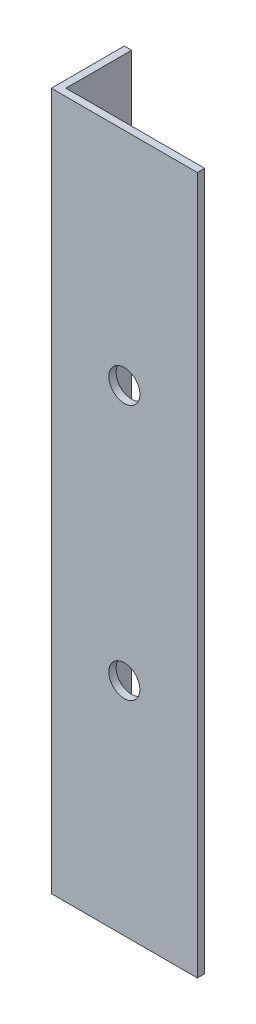
SolidWorks part; units mm, degrees
material "1060 Сплав"
ref_plane "Спереди" through (0, 0, 0) normal (0, 0, 1) x (1, 0, 0)
ref_plane "Сверху" through (0, 0, 0) normal (0, 1, 0) x (1, 0, 0)
ref_plane "Справа" through (0, 0, 0) normal (1, 0, 0) x (0, 0, -1)
sketch "Эскиз1" plane through (0, 0, 0) normal (0, 1, 0) x (1, 0, 0)
  line L0 (0, 0) -> (0, 20)
  line L1 (0, 20) -> (2, 20)
  line L2 (2, 20) -> (2, 2)
  line L3 (2, 2) -> (40, 2)
  line L4 (40, 2) -> (40, 0)
  line L5 (40, 0) -> (0, 0)
  dimension "D1" = 2
  dimension "D2" = 40
  dimension "D3" = 20
extrude "Бобышка-Вытянуть1" add sketch "Эскиз1" along normal blind 191
sketch "Эскиз2" plane through (0, 0, 0) normal (0, 0, 1) x (1, 0, 0)
  line L0 (20, 191) -> (20, 0) construction
  line L1 (0, 191) -> (40, 191) construction
  line L2 (0, 0) -> (40, 0) construction
  line L3 (0, 95.5) -> (40, 95.5) construction
  line L6 (0, 191) -> (0, 0) construction
  line L7 (40, 191) -> (40, 0) construction
  circle A1 centre (20, 130.5) radius 4.25
  circle A3 centre (20, 60.5) radius 4.25
  dimension "D1" = 70
  dimension "D2" = 35
  dimension "D4" = 8.5
extrude "Вырез-Вытянуть1" cut sketch "Эскиз2" against normal through all
sketch "Эскиз3" plane through (2, 0, 0) normal (1, 0, 0) x (0, 0, -1)
  circle A0 centre (10, 12) radius 2.25 construction
  circle A1 centre (10, 12) radius 2.25
  circle A2 centre (10, 179) radius 2.25 construction
  circle A3 centre (10, 179) radius 2.25
extrude "Вырез-Вытянуть2" cut sketch "Эскиз3" against normal through all
